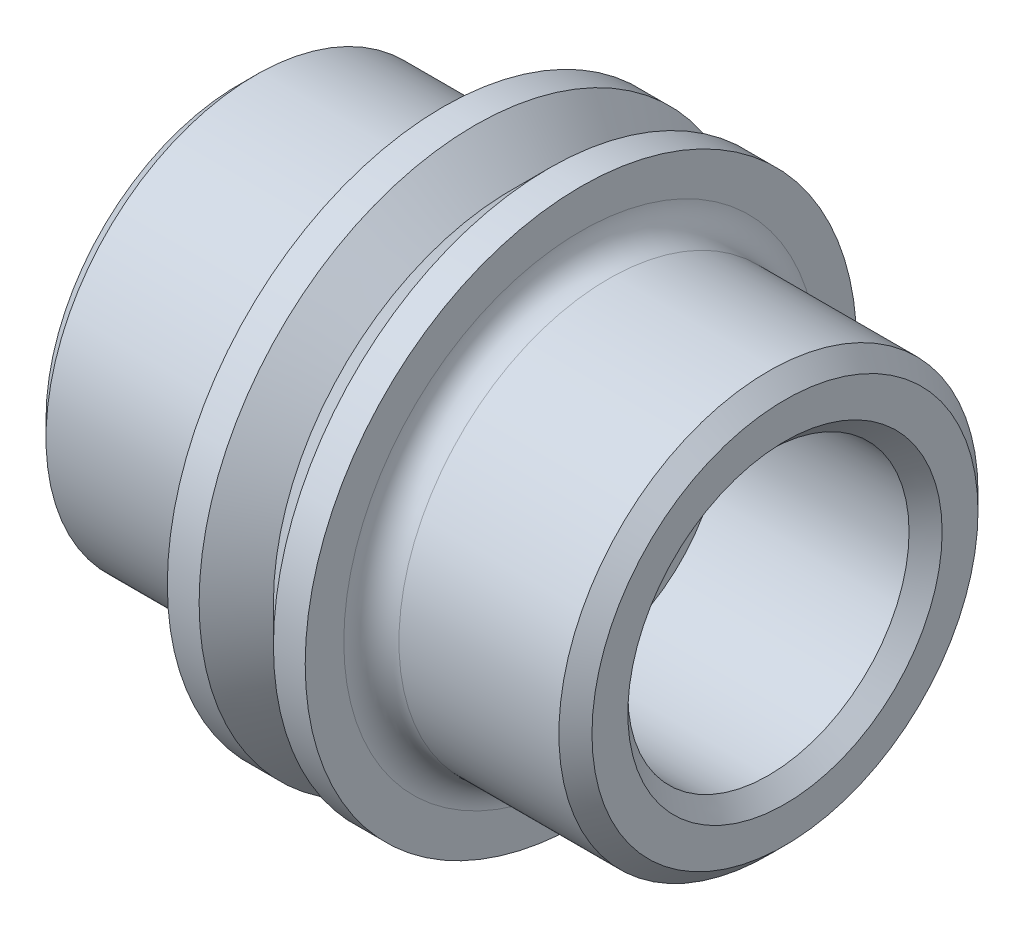
SolidWorks part; units mm, degrees
ref_plane "Front Plane" through (0, 0, 0) normal (0, 0, 1) x (1, 0, 0)
ref_plane "Top Plane" through (0, 0, 0) normal (0, 1, 0) x (1, 0, 0)
ref_plane "Right Plane" through (0, 0, 0) normal (1, 0, 0) x (0, 0, -1)
sketch "Sketch1" plane through (0, 0, 0) normal (1, 0, 0) x (0, 0, -1)
  circle A0 centre (0, 0) radius 6.35
  dimension "D1" = 12.7
extrude "Boss-Extrude1" add sketch "Sketch1" along normal mid plane 3.175
sketch "Sketch2" plane through (0, 0, 0) normal (1, 0, 0) x (0, 0, -1)
  circle A0 centre (0, 0) radius 4.826
  circle A1 centre (0, 0) radius 3.2385
  dimension "D1" = 1.5875
  dimension "D2" = 6.477
extrude "Boss-Extrude2" add sketch "Sketch2" along normal mid plane 12.573
sketch "Sketch3" plane through (0, 0, 0) normal (1, 0, 0) x (0, 0, -1)
  circle A0 centre (0, 0) radius 6.35
  dimension "D1" = 12.7
sketch "Sketch7" plane through (0, 0, 0) normal (0, 1, 0) x (1, 0, 0)
  line L0 (1.27, -6.7644) -> (-1.27, -6.7644)
  line L1 (-1.27, -6.7644) -> (0, -5.4944)
  line L2 (0, -5.4944) -> (1.27, -6.7644)
  line L3 (0, -6.35) -> (0, 6.35) construction
  point P5 (0, 0)
  point P6 (0, -6.7644)
  dimension "D1" = 2.54
  dimension "D2" = 1.27
chamfer "Chamfer1" distance 0.381 angle 45 4 edges at (-6.2865, 0, -3.2385) (6.2865, 0, -3.2385) (-6.2865, 0, -4.826) (6.2865, 0, -4.826)
fillet "Fillet2" radius 0.635 2 edges at (-1.5875, 0, -4.826) (1.5875, 0, -4.826)
sweep "Cut-Sweep1" cut profiles "Sketch7" path "Sketch3"
